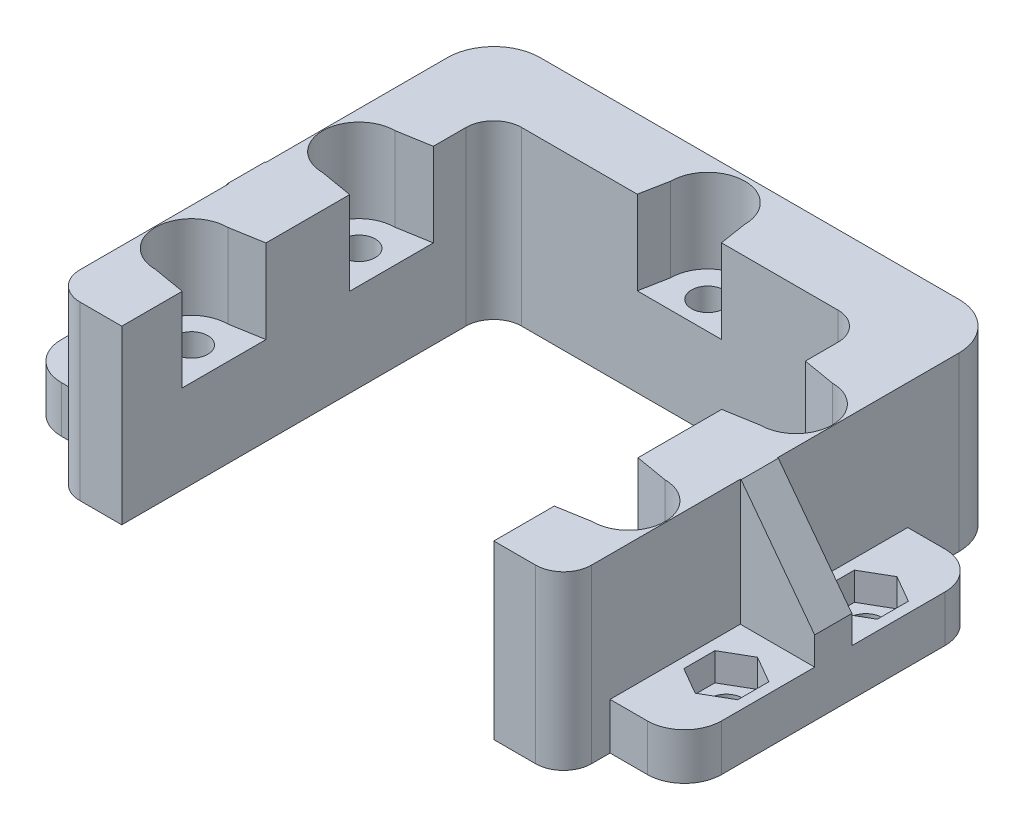
SolidWorks part; units mm, degrees
ref_plane "Front Plane" through (0, 0, 0) normal (0, 0, 1) x (1, 0, 0)
ref_plane "Top Plane" through (0, 0, 0) normal (0, 1, 0) x (1, 0, 0)
ref_plane "Right Plane" through (0, 0, 0) normal (1, 0, 0) x (0, 0, -1)
sketch "Sketch1" plane through (0, 0, 0) normal (0, 1, 0) x (1, 0, 0)
  line L0 (-20, -20) -> (-24.5, -20)
  line L1 (-17, 20) -> (17, 20)
  line L2 (-20, 17) -> (-20, -20)
  line L4 (20, 17) -> (20, -20)
  line L5 (-20, 20) -> (20, -20) construction
  line L6 (-20, -20) -> (20, 20) construction
  line L7 (-22.5, 27.5) -> (22.5, 27.5)
  line L8 (-27.5, 22.5) -> (-27.5, -17)
  line L10 (27.5, 22.5) -> (27.5, -17)
  line L11 (-27.5, 27.5) -> (27.5, -27.5) construction
  line L12 (-27.5, -27.5) -> (27.5, 27.5) construction
  line L13 (20, -20) -> (24.5, -20)
  arc A0 (17, 20) -> (20, 17) centre (17, 17) cw
  arc A1 (-17, 20) -> (-20, 17) centre (-17, 17) ccw
  arc A2 (22.5, 27.5) -> (27.5, 22.5) centre (22.5, 22.5) cw
  arc A3 (-22.5, 27.5) -> (-27.5, 22.5) centre (-22.5, 22.5) ccw
  arc A4 (24.5, -20) -> (27.5, -17) centre (24.5, -17) ccw
  arc A5 (-24.5, -20) -> (-27.5, -17) centre (-24.5, -17) cw
  point P0 (0, 0)
  point P12 (0, 0)
  dimension "D3" = 3
  dimension "D6" = 5
  dimension "D7" = 3
  dimension "D1" = 40
  dimension "D2" = 40
  dimension "D4" = 55
  dimension "D5" = 55
extrude "Boss-Extrude1" add sketch "Sketch1" along normal blind 18.5
sketch "Sketch2" plane through (0, 18.5, 0) normal (0, 1, 0) x (1, 0, 0)
  line L0 (-23.5, -9) -> (23.5, -9) construction
  line L1 (0, -9) -> (0, -20) construction
  line L4 (-20, -20) -> (20, -20) construction
  line L5 (0, 20) -> (0, 23) construction
  line L6 (-17, 20) -> (17, 20) construction
  line L7 (-23.5, 9) -> (23.5, 9) construction
  line L8 (0, 9) -> (0, 20) construction
  circle A0 centre (-23.5, -9) radius 1.75
  circle A1 centre (23.5, -9) radius 1.75
  circle A2 centre (0, 23) radius 1.75
  circle A3 centre (-23.5, 9) radius 1.75
  circle A4 centre (23.5, 9) radius 1.75
  dimension "D3" = 3.5
  dimension "D4" = 3.5
  dimension "D6" = 3.5
  dimension "D9" = 3.5
  dimension "D10" = 3.5
  dimension "D1" = 11
  dimension "D2" = 47
  dimension "D5" = 3
  dimension "47" = 47
  dimension "D8" = 11
extrude "Cut-Extrude1" cut sketch "Sketch2" against normal blind 15.5
sketch "Sketch3" plane through (0, 0, 0) normal (0, -1, 0) x (1, 0, 0)
  line L1 (-20.6, 7.3257) -> (-20.6, 10.6743)
  line L2 (-20.6, 10.6743) -> (-23.5, 12.3486)
  line L3 (-23.5, 12.3486) -> (-26.4, 10.6743)
  line L4 (-26.4, 10.6743) -> (-26.4, 7.3257)
  line L5 (-26.4, 7.3257) -> (-23.5, 5.6514)
  line L6 (-23.5, 5.6514) -> (-20.6, 7.3257)
  line L7 (23.4997, 5.6514) -> (26.3998, 7.3254)
  line L8 (26.3998, 7.3254) -> (26.4002, 10.674)
  line L9 (26.4002, 10.674) -> (23.5003, 12.3486)
  line L10 (23.5003, 12.3486) -> (20.6002, 10.6746)
  line L11 (20.6002, 10.6746) -> (20.5998, 7.326)
  line L12 (20.5998, 7.326) -> (23.4997, 5.6514)
  line L13 (3.3486, -23) -> (1.6743, -20.1)
  line L14 (1.6743, -20.1) -> (-1.6743, -20.1)
  line L15 (-1.6743, -20.1) -> (-3.3486, -23)
  line L16 (-3.3486, -23) -> (-1.6743, -25.9)
  line L17 (-1.6743, -25.9) -> (1.6743, -25.9)
  line L18 (1.6743, -25.9) -> (3.3486, -23)
  line L19 (-23.4997, -5.6514) -> (-26.3998, -7.3254)
  line L20 (-26.3998, -7.3254) -> (-26.4002, -10.674)
  line L21 (-26.4002, -10.674) -> (-23.5003, -12.3486)
  line L22 (-23.5003, -12.3486) -> (-20.6002, -10.6746)
  line L23 (-20.6002, -10.6746) -> (-20.5998, -7.326)
  line L24 (-20.5998, -7.326) -> (-23.4997, -5.6514)
  line L25 (23.4997, -5.6514) -> (20.5998, -7.326)
  line L26 (20.5998, -7.326) -> (20.6002, -10.6746)
  line L27 (20.6002, -10.6746) -> (23.5003, -12.3486)
  line L28 (23.5003, -12.3486) -> (26.4002, -10.674)
  line L29 (26.4002, -10.674) -> (26.3998, -7.3254)
  line L30 (26.3998, -7.3254) -> (23.4997, -5.6514)
  circle A0 centre (-23.5, 9) radius 2.9 construction
  circle A1 centre (23.5, 9) radius 2.9 construction
  circle A2 centre (0, -23) radius 2.9 construction
  circle A3 centre (-23.5, -9) radius 2.9 construction
  circle A4 centre (23.5, -9) radius 2.9 construction
  dimension "D1" = 5.8
  dimension "D2" = 5.8
  dimension "D3" = 5.8
  dimension "D4" = 5.8
  dimension "D5" = 5.8
extrude "Cut-Extrude2" cut sketch "Sketch3" against normal blind 3
sketch "Sketch4" plane through (-27.5, 0, 0) normal (-1, 0, 0) x (0, 0, 1)
  line L0 (-22.5, 0) -> (17, 0) construction
  line L1 (-17, 0) -> (15, 0)
  line L2 (-17, 0) -> (-17, 5)
  line L3 (-17, 5) -> (15, 5)
  line L4 (15, 0) -> (15, 5)
  line L5 (20, 18.5) -> (20, 0) construction
  dimension "D1" = 5
  dimension "D2" = 32
  dimension "D3" = 5
extrude "Boss-Extrude2" add sketch "Sketch4" along normal blind 8
fillet "Fillet1" radius 4 2 edges at (-35.5, 2.5, 15) (-35.5, 2.5, -17)
sketch "Sketch5" plane through (0, 5, 0) normal (0, 1, 0) x (1, 0, 0)
  line L0 (-35.5, 8.5) -> (-27.5, 8.5) construction
  line L1 (-35.5, -11) -> (-35.5, 13) construction
  line L2 (-27.5, 22.5) -> (-27.5, -17) construction
  line L3 (-31.5, 8.5) -> (-31.5, -6.5) construction
  line L4 (-31.5, 1) -> (-35.5, 1) construction
  circle A0 centre (-31.5, 8.5) radius 1.75
  circle A1 centre (-31.5, -6.5) radius 1.75
  dimension "D1" = 3.5
  dimension "D2" = 3.5
  dimension "D3" = 15
extrude "Cut-Extrude3" cut sketch "Sketch5" against normal blind 6
sketch "Sketch6" plane through (-27.5, 0, 0) normal (-1, 0, 0) x (0, 0, 1)
  line L0 (11, 5) -> (-13, 5) construction
  line L1 (-3, 5) -> (1, 5)
  line L2 (-3, 5) -> (-3, 18.5)
  line L3 (-3, 18.5) -> (1, 18.5)
  line L4 (1, 5) -> (1, 18.5)
  line L5 (-22.5, 18.5) -> (17, 18.5) construction
  dimension "D1" = 4
  dimension "D2" = 14
  dimension "D3" = 14
extrude "Boss-Extrude3" add sketch "Sketch6" along normal blind 8
chamfer "Chamfer1" distance 10.5 angle 37 1 edges at (-35.5, 18.5, -1)
sketch "Sketch7" plane through (0, 5, 0) normal (0, 1, 0) x (1, 0, 0)
  line L1 (-31.5, 11.8486) -> (-34.4, 10.1743)
  line L2 (-34.4, 10.1743) -> (-34.4, 6.8257)
  line L3 (-34.4, 6.8257) -> (-31.5, 5.1514)
  line L4 (-31.5, 5.1514) -> (-28.6, 6.8257)
  line L5 (-28.6, 6.8257) -> (-28.6, 10.1743)
  line L6 (-28.6, 10.1743) -> (-31.5, 11.8486)
  line L7 (-31.5, -3.1514) -> (-34.4, -4.8257)
  line L8 (-34.4, -4.8257) -> (-34.4, -8.1743)
  line L9 (-34.4, -8.1743) -> (-31.5, -9.8486)
  line L10 (-31.5, -9.8486) -> (-28.6, -8.1743)
  line L11 (-28.6, -8.1743) -> (-28.6, -4.8257)
  line L12 (-28.6, -4.8257) -> (-31.5, -3.1514)
  circle A0 centre (-31.5, 8.5) radius 2.9 construction
  circle A1 centre (-31.5, -6.5) radius 2.9 construction
  dimension "D1" = 5.8
  dimension "D2" = 5.8
extrude "Cut-Extrude4" cut sketch "Sketch7" against normal blind 3
mirror "Mirror1" about plane through (0, 0, 0) normal (1, 0, 0) of "Cut-Extrude4", "Chamfer1", "Boss-Extrude3", "Cut-Extrude3", "Fillet1", "Boss-Extrude2"
sketch "Sketch8" plane through (0, 18.5, 0) normal (0, 1, 0) x (1, 0, 0)
  line L0 (-4, 23) -> (-4.5746, 20)
  line L1 (-17, 20) -> (17, 20) construction
  line L2 (-4.5746, 20) -> (4.4783, 20)
  line L3 (4.4783, 20) -> (4, 23)
  line L4 (23.5, 12.9) -> (20, 13.5)
  line L5 (20, 17) -> (20, -20) construction
  line L6 (20, 13.5) -> (20, 4.5)
  line L7 (20, 4.5) -> (23.5, 5.1)
  line L8 (23.5, -5.1) -> (20, -4.5)
  line L9 (20, -4.5) -> (20, -13.5)
  line L10 (20, -13.5) -> (23.5, -12.9)
  line L11 (-23.5, -12.9) -> (-20, -13.5)
  line L12 (-20, -20) -> (-20, 17) construction
  line L13 (-20, -13.5) -> (-20, -4.5)
  line L14 (-20, -4.5) -> (-23.5, -5.1)
  line L15 (-20, -9) -> (-23.5, -9) construction
  line L16 (20, -9) -> (23.5, -9) construction
  line L17 (20, 9) -> (23.5, 9) construction
  line L18 (-0.0481, 20) -> (0, 23) construction
  line L19 (-23.5, 12.9) -> (-20, 13.5)
  line L20 (-20, 13.5) -> (-20, 4.5)
  line L21 (-20, 4.5) -> (-23.5, 5.1)
  line L22 (-23.5, 9) -> (-20, 9) construction
  arc A0 (4, 23) -> (-4, 23) centre (0, 23) ccw
  arc A1 (-23.5, 12.9) -> (-23.5, 5.1) centre (-23.5, 9) ccw
  arc A2 (-23.5, -5.1) -> (-23.5, -12.9) centre (-23.5, -9) ccw
  arc A4 (23.5, -12.9) -> (23.5, -5.1) centre (23.5, -9) ccw
  arc A5 (23.5, 5.1) -> (23.5, 12.9) centre (23.5, 9) ccw
  dimension "D1" = 9
  dimension "D2" = 9
  dimension "D3" = 9
  dimension "D4" = 9
extrude "Cut-Extrude7" cut sketch "Sketch8" against normal blind 9
